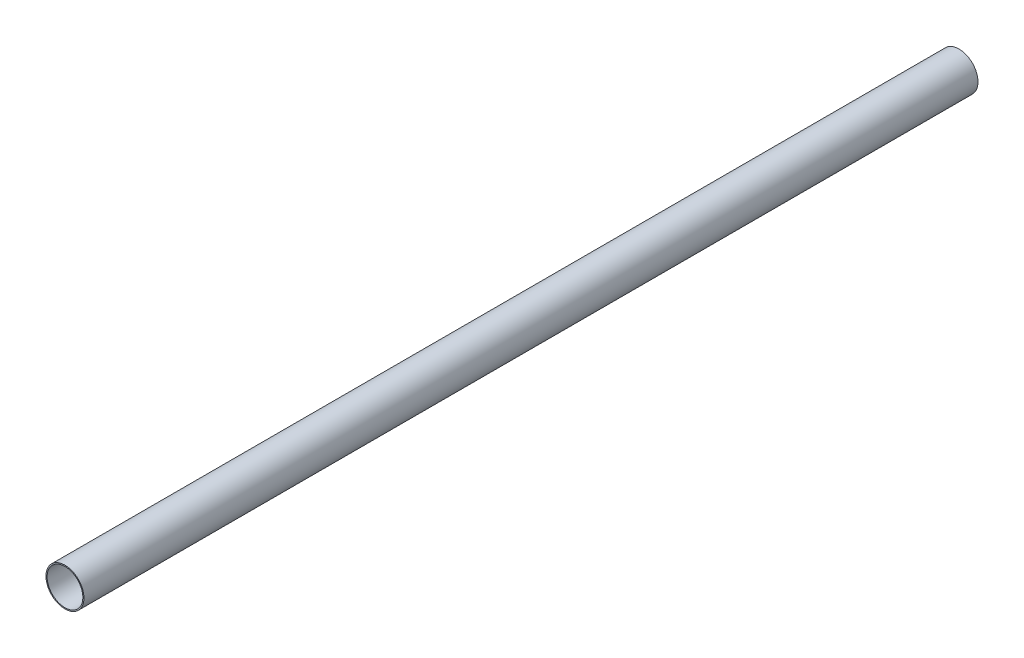
SolidWorks part; units mm, degrees
ref_plane "Alzado" through (0, 0, 0) normal (0, 0, 1) x (1, 0, 0)
ref_plane "Planta" through (0, 0, 0) normal (0, 1, 0) x (1, 0, 0)
ref_plane "Vista lateral" through (0, 0, 0) normal (1, 0, 0) x (0, 0, -1)
sketch "Croquis1" plane through (0, 0, 0) normal (0, 0, 1) x (1, 0, 0)
  circle A0 centre (0, 0) radius 4.25
  circle A1 centre (0, 0) radius 4
  dimension "D1" = 8.5
  dimension "D2" = 8
extrude "Saliente-Extruir1" add sketch "Croquis1" along normal blind 200
